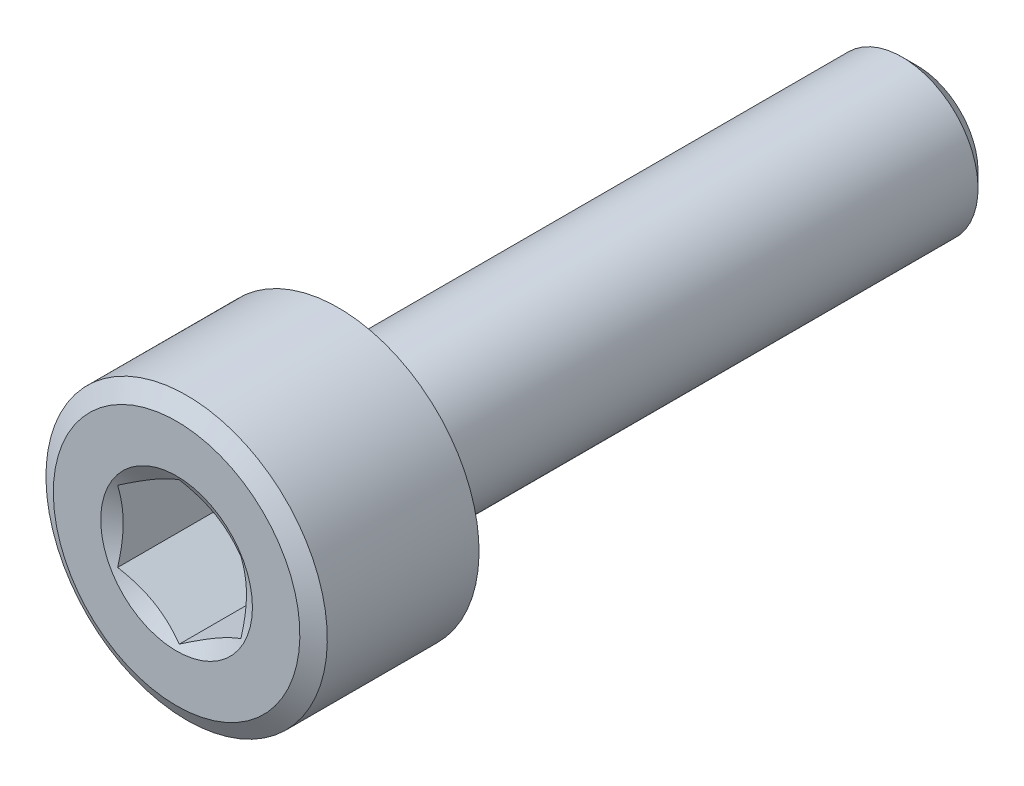
SolidWorks part; units mm, degrees
ref_plane "Front Plane" through (0, 0, 0) normal (0, 0, 1) x (1, 0, 0)
ref_plane "Top Plane" through (0, 0, 0) normal (0, 1, 0) x (1, 0, 0)
ref_plane "Right Plane" through (0, 0, 0) normal (1, 0, 0) x (0, 0, -1)
sketch "Sketch1" plane through (0, 0, 0) normal (1, 0, 0) x (0, 0, -1)
  line L0 (0, 0) -> (39.06, 0) construction
  line L1 (0, 0) -> (0, 6.5)
  line L2 (0, 6.5) -> (0.53, 7.418)
  line L3 (0.53, 7.418) -> (8.53, 7.418)
  line L4 (8.53, 7.418) -> (9.06, 6.5)
  line L5 (9.06, 6.5) -> (9.06, 4)
  line L6 (9.06, 4) -> (39.06, 4)
  line L7 (39.06, 4) -> (39.06, 0)
  line L8 (39.06, 0) -> (0, 0)
  dimension "D1" = 30
  dimension "D2" = 30
  dimension "D3" = 8
  dimension "D4" = 30
  dimension "D5" = 4
  dimension "D6" = 6.5
  dimension "D7" = 0.53
  dimension "D8" = 0.53
revolve "Revolve1" add sketch "Sketch1" angle 360 about L0
chamfer "Chamfer1" distance 0.8 angle 45 1 edges at (0, -4, -39.06)
sketch "Sketch2" plane through (0, 0, 0) normal (0, 0, 1) x (1, 0, 0)
  line L1 (3.25, -1.8764) -> (3.25, 1.8764)
  line L2 (3.25, 1.8764) -> (0, 3.7528)
  line L3 (0, 3.7528) -> (-3.25, 1.8764)
  line L4 (-3.25, 1.8764) -> (-3.25, -1.8764)
  line L5 (-3.25, -1.8764) -> (0, -3.7528)
  line L6 (0, -3.7528) -> (3.25, -1.8764)
  circle A0 centre (0, 0) radius 3.25 construction
  dimension "D1" = 6.5
extrude "Cut-Extrude1" cut sketch "Sketch2" against normal blind 6
sketch "Sketch3" plane through (0, 0, 0) normal (1, 0, 0) x (0, 0, -1)
  line L0 (0, 0) -> (10.8035, 0) construction
  line L1 (0, 0) -> (0, 4)
  line L2 (0, 6.5) -> (0, -6.5) construction
  line L3 (0, 4) -> (2.3094, 0)
  line L4 (2.3094, 0) -> (0, 0)
  line L5 (8.1667, 0) -> (6, 0)
  line L6 (6, 0) -> (6, 3.7528)
  line L7 (6, 3.7528) -> (8.1667, 0)
  dimension "D1" = 30
  dimension "D2" = 30
  dimension "D3" = 4
revolve "Cut-Revolve1" cut sketch "Sketch3" angle 360 about L0
sketch "Sketch9" plane through (0, 0, -39.06) normal (0, 0, -1) x (-1, 0, 0)
  circle A0 centre (0, 0) radius 4 construction
  circle A1 centre (0, 0) radius 4
curve "Helix/Spiral2" parameters "D10001"=28, "D30001"=8, "D40001"=1.25, "D10002"=2, "D30002"=16, "D40002"=1.25, "D50000"=1.25
sketch "Sketch11" plane through (0, 0, 0) normal (1, 0, 0) x (0, 0, -1)
  line L0 (39.06, 0) -> (43.8763, 0) construction
  line L1 (39.06, -3.2) -> (39.06, 3.2) construction
  line L2 (38.5054, 4.1956) -> (39.06, 3.235)
  line L3 (39.06, 3.235) -> (39.6146, 4.1956)
  line L4 (39.6146, 4.1956) -> (38.5054, 4.1956)
  point P7 (0, 0)
  dimension "D1" = 60
  dimension "D2" = 3.235
